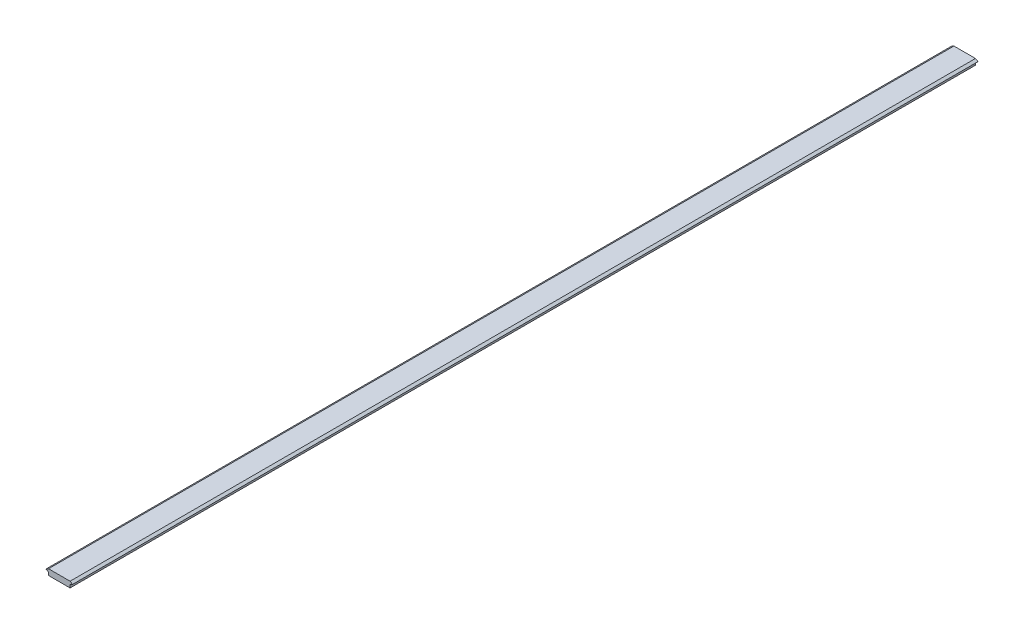
SolidWorks part; units mm, degrees
ref_plane "Front Plane" through (0, 0, 0) normal (0, 0, 1) x (1, 0, 0)
ref_plane "Top Plane" through (0, 0, 0) normal (0, 1, 0) x (1, 0, 0)
ref_plane "Right Plane" through (0, 0, 0) normal (1, 0, 0) x (0, 0, -1)
sketch "Sketch1" plane through (0, 0, 0) normal (0, 0, 1) x (1, 0, 0)
  line L0 (0, 0) -> (22, 0)
  line L1 (22, 0) -> (24.5981, -1.5)
  line L2 (24.5981, -1.5) -> (22, -3)
  line L3 (22, -3) -> (22, -6)
  line L4 (22, -6) -> (0, -6)
  line L5 (0, -6) -> (0, -3)
  line L6 (0, -3) -> (-2.5981, -1.5)
  line L7 (-2.5981, -1.5) -> (0, 0)
  dimension "D1" = 22
  dimension "D2" = 3
  dimension "D3" = 60
  dimension "D4" = 3
  dimension "D5" = 4.5
extrude "Boss-Extrude1" add sketch "Sketch1" along normal blind 925
equation "\"SlotWidth\"= 22mm"
equation "\"WedgeAngle\"= 60deg"
equation "\"WedgeHeight\"= 3mm"
equation "\"WedgeMidDistance\" = 4.5mm"
equation "\"WedgeDistance\"= 3mm"
equation "\"D1@Sketch1\"= \"SlotWidth\""
equation "\"D2@Sketch1\"= \"WedgeHeight\""
equation "\"D3@Sketch1\"= \"WedgeAngle\""
equation "\"D4@Sketch1\"= \"WedgeDistance\""
equation "\"D5@Sketch1\"= \"WedgeMidDistance\""
equation "\"AxialLength\"= 925mm"
equation "\"D1@Boss-Extrude1\"= \"AxialLength\""
